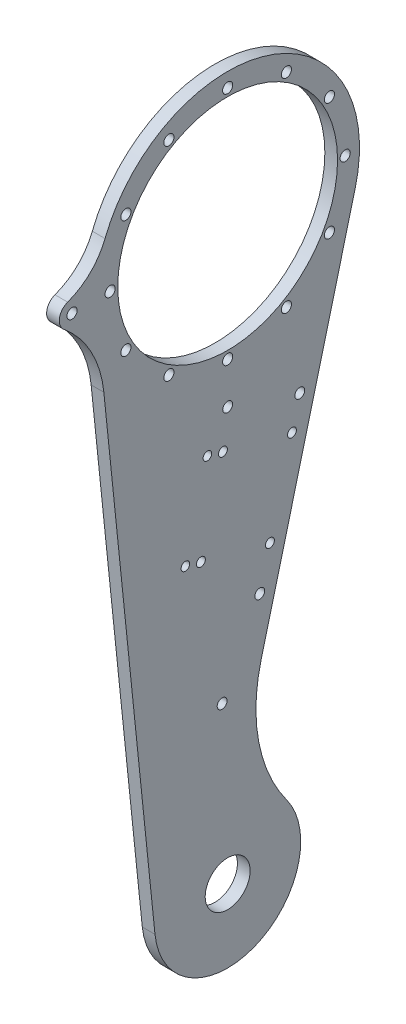
SolidWorks part; units mm, degrees
material "Thornel Mat VMA"
ref_plane "前视基准面" through (0, 0, 0) normal (0, 0, 1) x (1, 0, 0)
ref_plane "上视基准面" through (0, 0, 0) normal (0, 1, 0) x (1, 0, 0)
ref_plane "右视基准面" through (0, 0, 0) normal (1, 0, 0) x (0, 0, -1)
sketch "草图1" plane through (0, 0, 0) normal (1, 0, 0) x (0, 0, -1)
  line L0 (40.1598, -10.4615) -> (1.9651, -157.0841)
  line L1 (-41.2802, -4.2653) -> (-22.8782, -182.3639)
  circle A0 centre (0, 0) radius 41.5
  circle A1 centre (0, -180) radius 23
  dimension "D1" = 83
  dimension "D2" = 46
  dimension "D3" = 180
  dimension "D4" = 20.5
extrude "凸台-拉伸1" add sketch "草图1" along normal blind 4 contours A0 | A1 L0 A0 L1 | A1
sketch "草图3" plane through (0, 0, 0) normal (-1, 0, 0) x (0, 0, 1)
  circle A0 centre (0, 0) radius 34.6
  circle A1 centre (0, -180) radius 7.075
  arc A2 (-1.9651, -157.0841) -> (22.8782, -182.3639) centre (0, -180) ccw construction
  dimension "D1" = 69.2
  dimension "D2" = 14.15
extrude "切除-拉伸2" cut sketch "草图3" against normal blind 5
sketch "草图2" plane through (0, 0, 0) normal (-1, 0, 0) x (0, 0, 1)
  line L0 (0, 37) -> (0, 0) construction
  circle A0 centre (0, 0) radius 37
  circle A1 centre (0, 37) radius 1.6
  circle A2 centre (0, 0) radius 34.6 construction
  dimension "D1" = 74
  dimension "D2" = 3.2
extrude "切除-拉伸1" cut sketch "草图2" against normal blind 5 contours A0 A1 | L0 A0 A1 | A0 L0 A1
pattern_circular "阵列(圆周)1" count 12 over 360 about axis through (0, 0, 0) along (1, 0, 0) of "切除-拉伸1"
fillet "圆角1" radius 50 1 edges at (2, -157.0841, -1.9651)
sketch "草图4" plane through (4, 0, 0) normal (1, 0, 0) x (0, 0, -1)
  line L0 (22.7171, -57.5863) -> (27.5556, -58.8467) construction
  line L1 (22.7171, -57.5863) -> (10.1129, -105.9716) construction
  line L4 (40.1598, -10.4615) -> (10.5134, -124.2687) construction
  circle A1 centre (22.7171, -57.5863) radius 1.55
  circle A3 centre (10.1129, -105.9716) radius 1.55
  circle A6 centre (0, 0) radius 34.6 construction
  dimension "D2" = 3.1
  dimension "D3" = 50
  dimension "D4" = 3.1
  dimension "D1" = 5
  dimension "D6" = 50
extrude "切除-拉伸3" cut sketch "草图4" against normal blind 10
sketch "草图5" plane through (4, 0, 0) normal (1, 0, 0) x (0, 0, -1)
  line L0 (-49, 0) -> (-37, 0) construction
  line L1 (-49, 4) -> (-37, 4)
  line L2 (-49, -4) -> (-37, -4)
  arc A0 (-49, 4) -> (-49, -4) centre (-49, 0) ccw
  arc A1 (-37, -4) -> (-37, 4) centre (-37, 0) ccw
  circle A2 centre (-37, 0) radius 1.6 construction
  circle A3 centre (-37, 0) radius 1.6
  circle A4 centre (-49, 0) radius 1.6
  circle A5 centre (0, 0) radius 34.6 construction
  point P2 (-43, 0)
  dimension "D1" = 4
  dimension "D3" = 3.2
  dimension "D4" = 3.2
  dimension "D5" = 37
  dimension "D2" = 12
extrude "凸台-拉伸2" add sketch "草图5" against normal blind 4
fillet "圆角2" radius 20 1 edges at (2, 4, 41.3068)
sketch "草图6" plane through (4, 0, 0) normal (1, 0, 0) x (0, 0, -1)
  line L0 (-1.746, -130) -> (0, -180) construction
  line L1 (0, -180) -> (0, 0) construction
  circle A0 centre (0, -50) radius 1.55
  circle A1 centre (0, 0) radius 34.6 construction
  circle A2 centre (-1.746, -130) radius 1.55
  circle A3 centre (0, -180) radius 7.075 construction
  dimension "D1" = 3.1
  dimension "D2" = 50
  dimension "D3" = 50
  dimension "D4" = 3.1
  dimension "D5" = 2
extrude "切除-拉伸4" cut sketch "草图6" against normal blind 10
fillet "圆角3" radius 35 1 edges at (2, -4, 41.3068)
sketch "草图7" plane through (4, 0, 0) normal (1, 0, 0) x (0, 0, -1)
  line L0 (20.236, -67.1106) -> (13.3037, -93.7225) construction
  line L1 (40.1598, -10.4615) -> (10.5134, -124.2687) construction
  line L2 (-1.4935, -61.4501) -> (20.236, -67.1106) construction
  circle A0 centre (5.9051, -77.5863) radius 17.7515
  circle A1 centre (-1.4935, -61.4501) radius 1.4
  circle A2 centre (20.236, -67.1106) radius 1.4
  circle A3 centre (-8.4258, -88.062) radius 1.4
  circle A4 centre (13.3037, -93.7225) radius 1.4
  circle A7 centre (22.7171, -57.5863) radius 1.55 construction
  dimension "D1" = 2.8
  dimension "D2" = 2.8
  dimension "D3" = 2.8
  dimension "D4" = 2.8
  dimension "D5" = 27.5
  dimension "D9" = 20
  dimension "D6" = 35.503
  dimension "D7" = 27.5
  dimension "D8" = 5
extrude "切除-拉伸5" cut sketch "草图7" against normal blind 10 contours A0 A2 | A0 A2 | A0 A1 | A0 A1 | A0 A3 | A0 A3 | A0 A4 | A0 A4
sketch "草图8" plane through (4, 0, 0) normal (1, 0, 0) x (0, 0, -1)
  line L0 (-6.3759, -60.1783) -> (20.236, -67.1106) construction
  line L1 (40.1598, -10.4615) -> (10.5134, -124.2687) construction
  line L2 (-13.3082, -86.7902) -> (13.3037, -93.7225) construction
  circle A0 centre (-6.3759, -60.1783) radius 1.35
  circle A1 centre (-13.3082, -86.7902) radius 1.35
  circle A2 centre (20.236, -67.1106) radius 1.4 construction
  circle A3 centre (13.3037, -93.7225) radius 1.4 construction
  dimension "D1" = 2.7
  dimension "D3" = 2.7
  dimension "D2" = 27.5
  dimension "D4" = 27.5
extrude "切除-拉伸6" cut sketch "草图8" against normal blind 10
